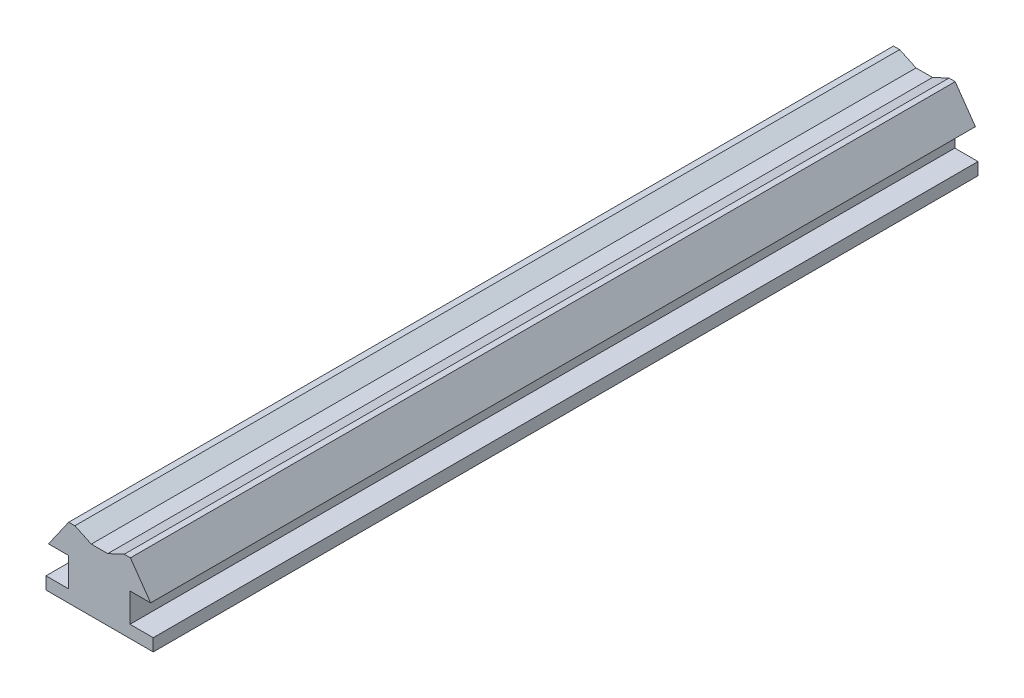
SolidWorks part; units mm, degrees
ref_plane "Front Plane" through (0, 0, 0) normal (0, 0, 1) x (1, 0, 0)
ref_plane "Top Plane" through (0, 0, 0) normal (0, 1, 0) x (1, 0, 0)
ref_plane "Right Plane" through (0, 0, 0) normal (1, 0, 0) x (0, 0, -1)
sketch "Sketch2" plane through (0, 0, 0) normal (0, 0, 1) x (1, 0, 0)
  line L2 (-12.8072, -157.1849) -> (-7.8464, -157.1849)
  line L3 (-90.0501, 89.6927) -> (-50.2221, 71.1207)
  line L4 (-50.2221, 71.1207) -> (-10.2901, 71.1207)
  line L14 (29.6058, 89.7244) -> (44.6058, 89.7244)
  line L20 (-90.0501, 89.6927) -> (-105.0501, 89.6927)
  line L21 (-154.0908, 19.6552) -> (-105.211, 19.6552)
  line L22 (-105.211, 14.3343) -> (-105.2109, 14.3343)
  line L23 (-105.211, 19.6552) -> (-105.211, -50.3448)
  line L26 (-160.0501, -59.6248) -> (-160.0501, -80.3448)
  line L27 (93.6688, 19.6552) -> (43.6688, 19.6552)
  line L28 (-160.0501, -80.3448) -> (99.9499, -80.3448)
  line L30 (43.6688, 19.6552) -> (43.6688, -50.3448)
  line L31 (43.6688, -50.3448) -> (99.9499, -50.3448)
  line L32 (99.9499, -50.3448) -> (99.9499, -80.3448)
  line L33 (-154.0908, 19.6552) -> (-105.0501, 89.6927)
  line L36 (44.6058, 89.7244) -> (93.6688, 19.6552)
  line L37 (-30.2561, 71.1207) -> (-30.2561, -118.5037) construction
  line L38 (-105.211, -50.3448) -> (-160.0501, -50.3448)
  line L39 (29.6058, 89.7244) -> (-10.2901, 71.1207)
  line L40 (-160.0501, -50.3448) -> (-160.0501, -59.6248)
  point P11 (-30.0501, -94.6248)
  point P20 (-30.0501, -181.8646)
  point P27 (-30.0501, -181.8646)
  point P28 (-30.0501, 53.1354)
  point P30 (-30.2561, 71.1207)
  dimension "D1" = 155
  dimension "D3" = 155
  dimension "D4" = 15
  dimension "D5" = 15
  dimension "D6" = 125
  dimension "D7" = 85.5
  dimension "D8" = 125
  dimension "D9" = 50
  dimension "D10" = 70
  dimension "D11" = 70
  dimension "D12" = 30
extrude "Boss-Extrude3" add sketch "Sketch2" along normal blind 2000
